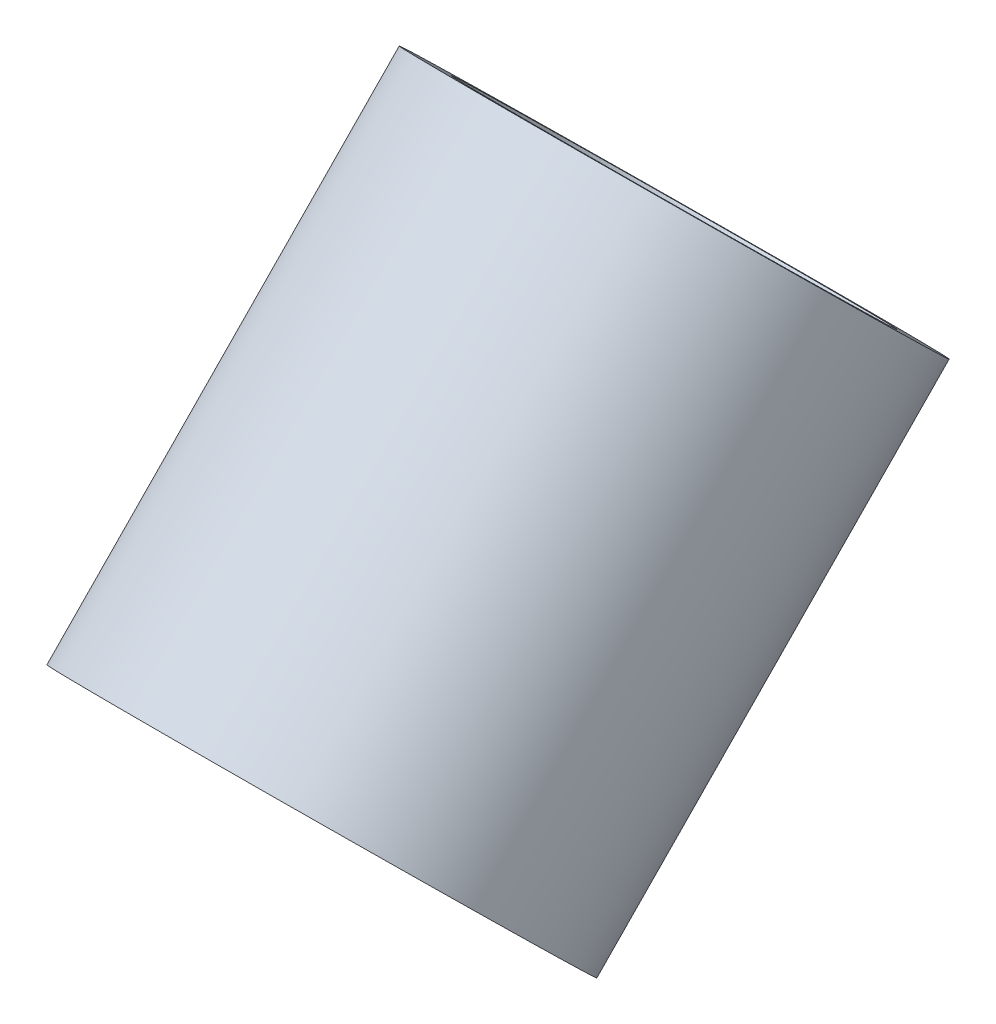
SolidWorks part; units mm, degrees
material "Cast Alloy Steel"
ref_plane "Front Plane" through (0, 0, 0) normal (0, 0, 1) x (1, 0, 0)
ref_plane "Top Plane" through (0, 0, 0) normal (0, 1, 0) x (1, 0, 0)
ref_plane "Right Plane" through (0, 0, 0) normal (1, 0, 0) x (0, 0, -1)
ref_plane "Plane1" through (0, -521.3142, 510.5086) normal (0, 0.7145, -0.6997) x (1, 0, 0)
sketch "Sketch3" plane through (0, -521.3142, 510.5086) normal (0, 0.7145, -0.6997) x (1, 0, 0)
  circle A0 centre (0, -1433.9409) radius 20.6375
  circle A1 centre (0, -1433.9409) radius 25.4
extrude "Boss-Extrude1" add sketch "Sketch3" along normal mid plane 57.15
